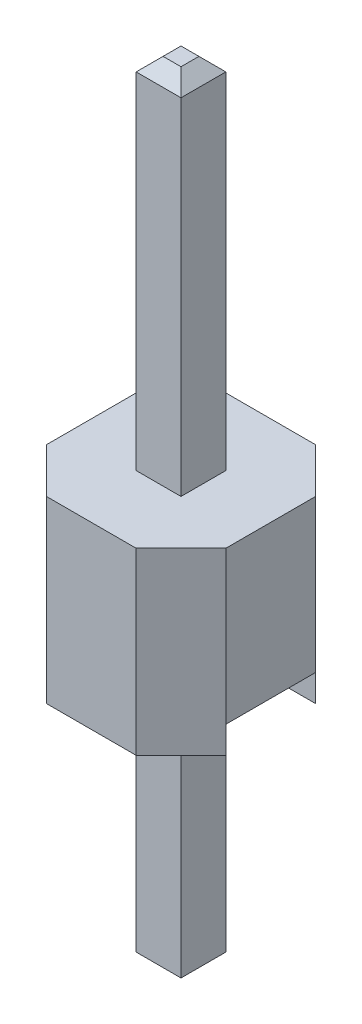
SolidWorks part; units mm, degrees
ref_plane "Front Plane" through (0, 0, 0) normal (0, 0, 1) x (1, 0, 0)
ref_plane "Top Plane" through (0, 0, 0) normal (0, 1, 0) x (1, 0, 0)
ref_plane "Right Plane" through (0, 0, 0) normal (1, 0, 0) x (0, 0, -1)
sketch "Sketch1" plane through (0, 0, 0) normal (0, 1, 0) x (1, 0, 0)
  line L0 (0.635, 1.27) -> (1.27, 0.635)
  line L1 (-0.635, -1.27) -> (0.635, -1.27)
  line L2 (-1.27, -0.635) -> (-1.27, 0.635)
  line L3 (-0.635, 1.27) -> (0.635, 1.27)
  line L4 (1.27, -0.635) -> (1.27, 0.635)
  line L5 (-0.9525, -0.9525) -> (0.9525, 0.9525) construction
  line L6 (-0.9525, 0.9525) -> (0.9525, -0.9525) construction
  line L7 (1.27, -0.635) -> (0.635, -1.27)
  line L8 (-0.635, -1.27) -> (-1.27, -0.635)
  line L9 (-1.27, 0.635) -> (-0.635, 1.27)
  point P0 (0, 0)
  point P17 (0, 0)
  dimension "D4" = 4
extrude "Boss-Extrude1" add sketch "Sketch1" along normal blind 2.54
sketch "Sketch2" plane through (1.27, 0, 0) normal (1, 0, 0) x (0, 0, -1)
  line L0 (-0.635, 0) -> (0.635, 0)
  line L2 (-0.635, 0) -> (-0.635, 0.381)
  line L3 (-0.635, 0.381) -> (0.635, 0.381)
  line L4 (0.635, 0) -> (0.635, 0.381)
  point P0 (0, 0)
extrude "Cut-Extrude1" cut sketch "Sketch2" against normal up to surface (2.54 mm away) up to face at (-1.27, 1.27, 0)
sketch "Sketch3" plane through (0, 2.54, 0) normal (0, 1, 0) x (1, 0, 0)
  line L1 (-0.3175, -0.3175) -> (0.3175, -0.3175)
  line L2 (-0.3175, -0.3175) -> (-0.3175, 0.3175)
  line L3 (-0.3175, 0.3175) -> (0.3175, 0.3175)
  line L4 (0.3175, -0.3175) -> (0.3175, 0.3175)
  line L5 (-0.3175, -0.3175) -> (0.3175, 0.3175) construction
  line L6 (-0.3175, 0.3175) -> (0.3175, -0.3175) construction
  point P0 (0, 0)
  dimension "D1" = 0.635
extrude "Boss-Extrude2" add sketch "Sketch3" along normal blind 5.08
chamfer "Chamfer1" distance 0.1905 angle 45 4 edges at (0, 7.62, -0.3175) (0.3175, 7.62, 0) (-0.3175, 7.62, 0) (0, 7.62, 0.3175)
sketch "Sketch4" plane through (0, 0.381, 0) normal (0, -1, 0) x (1, 0, 0)
  line L1 (-0.3175, -0.3175) -> (0.3175, -0.3175)
  line L2 (-0.3175, -0.3175) -> (-0.3175, 0.3175)
  line L3 (-0.3175, 0.3175) -> (0.3175, 0.3175)
  line L4 (0.3175, -0.3175) -> (0.3175, 0.3175)
  line L5 (-0.3175, -0.3175) -> (0.3175, 0.3175) construction
  line L6 (-0.3175, 0.3175) -> (0.3175, -0.3175) construction
  point P0 (0, 0)
  dimension "D1" = 0.635
extrude "Boss-Extrude3" add sketch "Sketch4" along normal blind 3.937
chamfer "Chamfer2" distance 0.1905 angle 45 4 edges at (-0.3175, -3.556, 0) (0, -3.556, -0.3175) (0.3175, -3.556, 0) (0, -3.556, 0.3175)
